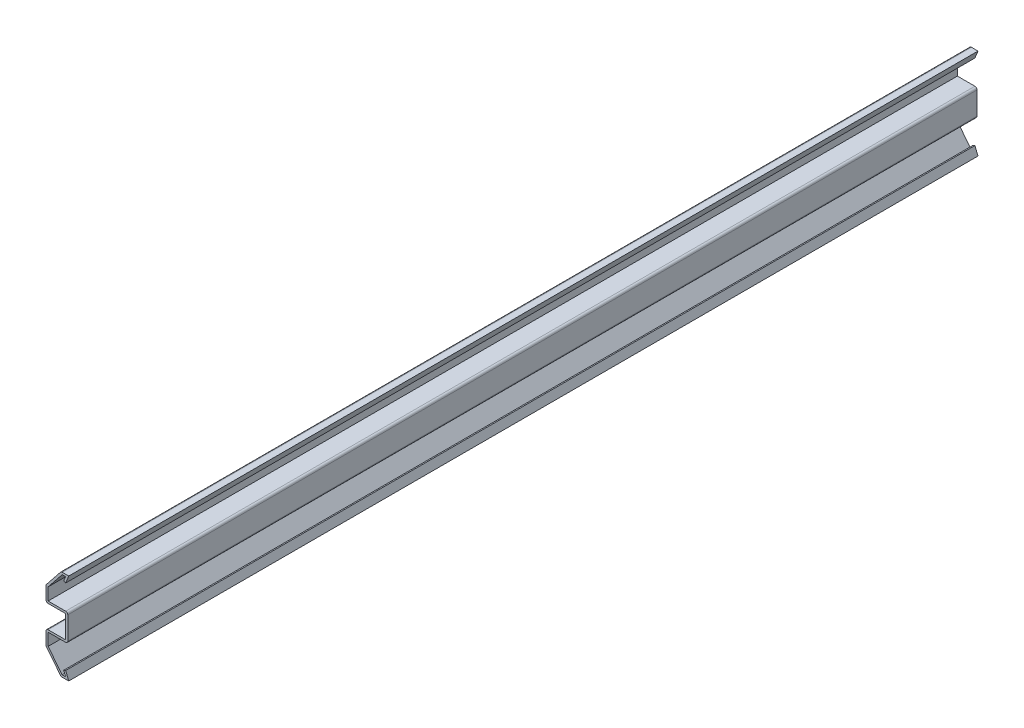
SolidWorks part; units mm, degrees
ref_plane "Front Plane" through (0, 0, 0) normal (0, 0, 1) x (1, 0, 0)
ref_plane "Top Plane" through (0, 0, 0) normal (0, 1, 0) x (1, 0, 0)
ref_plane "Right Plane" through (0, 0, 0) normal (1, 0, 0) x (0, 0, -1)
sketch "Sketch1" plane through (0, 0, 0) normal (0, 0, 1) x (1, 0, 0)
  line L0 (-3.9454, 0) -> (0, 0) construction
  line L1 (0, 0) -> (0, 19.05) construction
  line L2 (0, 19.05) -> (-2.7314, 19.05) construction
  line L3 (-1.2859, 3.175) -> (0, 0)
  line L4 (0, 0) -> (-3.175, 0)
  line L5 (-3.175, 0) -> (-9.525, 7.9375)
  line L6 (-9.525, 7.9375) -> (-9.525, 14.2875)
  line L7 (-9.525, 14.2875) -> (-1.2859, 14.2875)
  line L8 (-1.2859, 14.2875) -> (-1.2859, 23.8125)
  line L9 (-9.525, 23.8125) -> (-1.2859, 23.8125)
  line L10 (-9.525, 30.1625) -> (-9.525, 23.8125)
  line L11 (-3.175, 38.1) -> (-9.525, 30.1625)
  line L12 (0, 38.1) -> (-3.175, 38.1)
  line L13 (-1.2859, 34.925) -> (0, 38.1)
  point P10 (-2.4554, 0)
  point P14 (-1.2859, 19.05)
extrude "Extrude-Thin1" add sketch "Sketch1" against normal blind 381 thin
fillet "Fillet1" radius 0.889 8 edges at (-3.175, 0, -190.5) (-9.525, 7.9375, -190.5) (-9.525, 14.2875, -190.5) (-0.3969, 13.3985, -190.5) (-0.3969, 24.7015, -190.5) (-9.525, 23.8125, -190.5) (-9.525, 30.1625, -190.5) (-3.175, 38.1, -190.5)
equation "\"D1@Extrude-Thin1\"=\"D9@Sketch1\"*10"
